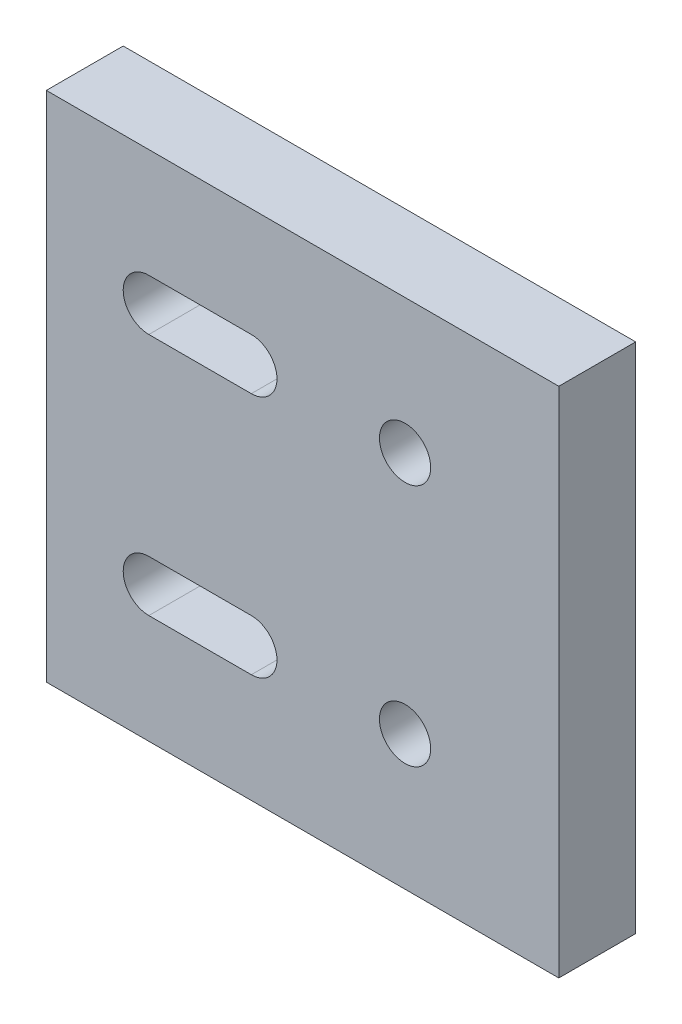
SolidWorks part; units mm, degrees
ref_plane "前视基准面" through (0, 0, 0) normal (0, 0, 1) x (1, 0, 0)
ref_plane "上视基准面" through (0, 0, 0) normal (0, 1, 0) x (1, 0, 0)
ref_plane "右视基准面" through (0, 0, 0) normal (1, 0, 0) x (0, 0, -1)
sketch "草图1" plane through (0, 0, 0) normal (0, 0, 1) x (1, 0, 0)
  line L0 (4, 26.603) -> (4, -19.7616) construction
  line L1 (10, -10) -> (-10, -10)
  line L2 (10, -10) -> (10, 10)
  line L3 (10, 10) -> (-10, 10)
  line L4 (-10, -10) -> (-10, 10)
  line L5 (10, -10) -> (-10, 10) construction
  line L6 (10, 10) -> (-10, -10) construction
  line L7 (-32.389, 0) -> (39.7229, 0) construction
  line L8 (-6, 4.75) -> (-2, 4.75) construction
  line L9 (-6, 5.75) -> (-2, 5.75)
  line L10 (-6, 3.75) -> (-2, 3.75)
  line L11 (-6, -4.75) -> (-2, -4.75) construction
  line L12 (-6, -5.75) -> (-2, -5.75)
  line L13 (-6, -3.75) -> (-2, -3.75)
  circle A0 centre (4, 4.75) radius 1
  circle A1 centre (4, -4.75) radius 1
  arc A2 (-6, 5.75) -> (-6, 3.75) centre (-6, 4.75) ccw
  arc A3 (-2, 3.75) -> (-2, 5.75) centre (-2, 4.75) ccw
  arc A4 (-6, -5.75) -> (-6, -3.75) centre (-6, -4.75) cw
  arc A5 (-2, -3.75) -> (-2, -5.75) centre (-2, -4.75) cw
  point P0 (0, 0)
  point P14 (-4, 4.75)
  point P23 (-4, -4.75)
  point P28 (8, -4.75)
  point P29 (8, -2.9134)
  dimension "D3" = 2
  dimension "D4" = 2
  dimension "D5" = 9.5
  dimension "D6" = 6
  dimension "D7" = 1
  dimension "D8" = 4
  dimension "D9" = 4
  dimension "D10" = 9.5
  dimension "D1" = 20
  dimension "D2" = 20
extrude "凸台-拉伸1" add sketch "草图1" along normal blind 3
